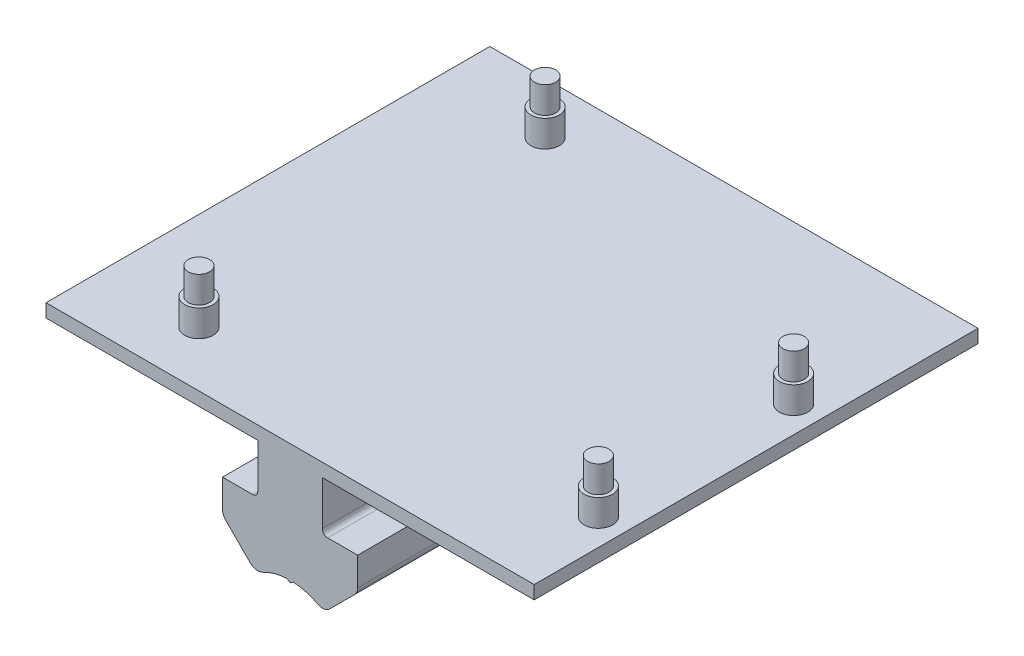
SolidWorks part; units mm, degrees
ref_plane "Front Plane" through (0, 0, 0) normal (0, 0, 1) x (1, 0, 0)
ref_plane "Top Plane" through (0, 0, 0) normal (0, 1, 0) x (1, 0, 0)
ref_plane "Right Plane" through (0, 0, 0) normal (1, 0, 0) x (0, 0, -1)
sketch "Sketch1" plane through (0, 0, 433.7261) normal (0, 0, 1) x (1, 0, 0)
  line L0 (12.2628, 63.4393) -> (12.8172, 63.4393)
  line L107 (14.5178, 67.9818) -> (14.5178, 70.5218)
  line L108 (14.5178, 70.5218) -> (-15.7882, 70.5218)
  line L109 (-15.7882, 70.5218) -> (-15.7882, 72.4268)
  line L110 (-15.7882, 72.4268) -> (54.0618, 72.4268)
  line L111 (54.0618, 72.4268) -> (54.0618, 70.5218)
  line L112 (54.0618, 70.5218) -> (23.7558, 70.5218)
  line L113 (23.7558, 70.5218) -> (23.7558, 67.9818)
  line L119 (23.7558, 67.9818) -> (23.7558, 64.1973)
  line L120 (24.5138, 63.4393) -> (28.8058, 63.4393)
  line L121 (28.8058, 63.4393) -> (28.8058, 59.4011)
  line L122 (28.3653, 58.3376) -> (24.8224, 54.7946)
  line L123 (19.5802, 55.4896) -> (19.1368, 55.1792)
  line L124 (19.1368, 55.1792) -> (18.6935, 55.4896)
  line L125 (13.4513, 54.7946) -> (9.9084, 58.3376)
  line L126 (9.4678, 59.4011) -> (9.4678, 63.4393)
  line L127 (9.4678, 63.4393) -> (12.2628, 63.4393)
  line L128 (12.2628, 63.4393) -> (12.54, 63.7165)
  line L129 (12.54, 63.7165) -> (12.8172, 63.4393)
  line L130 (12.8172, 63.4393) -> (13.7598, 63.4393)
  line L131 (14.5178, 64.1973) -> (14.5178, 67.9818)
  line L132 (23.7558, 67.9818) -> (23.7558, 64.1973)
  line L133 (24.5138, 63.4393) -> (28.8058, 63.4393)
  line L134 (28.8058, 63.4393) -> (28.8058, 59.4011)
  line L135 (28.3653, 58.3376) -> (24.8224, 54.7946)
  line L210 (19.5802, 55.4896) -> (19.1368, 55.1792)
  line L211 (19.1368, 55.1792) -> (18.6935, 55.4896)
  line L212 (13.4513, 54.7946) -> (9.9084, 58.3376)
  line L213 (9.4678, 59.4011) -> (9.4678, 63.4393)
  line L214 (9.4678, 63.4393) -> (12.2628, 63.4393)
  line L217 (12.8172, 63.4393) -> (13.7598, 63.4393)
  line L218 (14.5178, 64.1973) -> (14.5178, 67.9818)
  arc A73 (23.7558, 64.1973) -> (24.5138, 63.4393) centre (24.5138, 64.1973) ccw
  arc A74 (28.3653, 58.3376) -> (28.8058, 59.4011) centre (27.3018, 59.4011) ccw
  arc A75 (23.0557, 54.5287) -> (24.8224, 54.7946) centre (23.7589, 55.8581) ccw
  arc A76 (23.0557, 54.5287) -> (19.5802, 55.4896) centre (19.1368, 47.1203) ccw
  arc A77 (18.6935, 55.4896) -> (15.218, 54.5287) centre (19.1368, 47.1203) ccw
  arc A78 (13.4513, 54.7946) -> (15.218, 54.5287) centre (14.5148, 55.8581) ccw
  arc A79 (9.4678, 59.4011) -> (9.9084, 58.3376) centre (10.9718, 59.4011) ccw
  arc A80 (13.7598, 63.4393) -> (14.5178, 64.1973) centre (13.7598, 64.1973) ccw
  arc A81 (23.7558, 64.1973) -> (24.5138, 63.4393) centre (24.5138, 64.1973) ccw
  arc A82 (28.3653, 58.3376) -> (28.8058, 59.4011) centre (27.3018, 59.4011) ccw
  arc A83 (23.0557, 54.5287) -> (24.8224, 54.7946) centre (23.7589, 55.8581) ccw
  arc A84 (23.0557, 54.5287) -> (19.5802, 55.4896) centre (19.1368, 47.1203) ccw
  arc A85 (18.6935, 55.4896) -> (15.218, 54.5287) centre (19.1368, 47.1203) ccw
  arc A86 (13.4513, 54.7946) -> (15.218, 54.5287) centre (14.5148, 55.8581) ccw
  arc A87 (9.4678, 59.4011) -> (9.9084, 58.3376) centre (10.9718, 59.4011) ccw
  arc A88 (13.7598, 63.4393) -> (14.5178, 64.1973) centre (13.7598, 64.1973) ccw
  dimension "D2" = 69.85
  dimension "D3" = 1.905
  dimension "D4" = 2.54
  dimension "D1" = 0.381
extrude "Boss-Extrude1" add sketch "Sketch1" against normal blind 63.5
sketch "Sketch3" plane through (0, 72.4268, 0) normal (0, 1, 0) x (1, 0, 0)
  circle A0 centre (-0.5482, -377.5549) radius 1.524
  circle A1 centre (50.2518, -392.7949) radius 1.524
  circle A2 centre (50.2518, -420.7349) radius 1.524
  circle A3 centre (-1.8182, -425.8149) radius 1.524
  dimension "D1" = 3.048
extrude "Boss-Extrude2" add sketch "Sketch3" along normal blind 7.62
sketch "Sketch4" plane through (0, 72.4268, 0) normal (0, 1, 0) x (1, 0, 0)
  circle A2 centre (-0.5482, -377.5549) radius 2.032
  circle A3 centre (-0.5482, -377.5549) radius 2.032
  circle A5 centre (50.2518, -392.7949) radius 2.032
  circle A6 centre (50.2518, -392.7949) radius 2.032
  circle A8 centre (50.2518, -420.7349) radius 2.032
  circle A9 centre (50.2518, -420.7349) radius 2.032
  circle A11 centre (-1.8182, -425.8149) radius 2.032
  circle A12 centre (-1.8182, -425.8149) radius 2.032
  dimension "D1" = 0.508
  dimension "D2" = 0.508
  dimension "D3" = 0.508
  dimension "D4" = 0.508
extrude "Boss-Extrude3" add sketch "Sketch4" along normal blind 3.81
